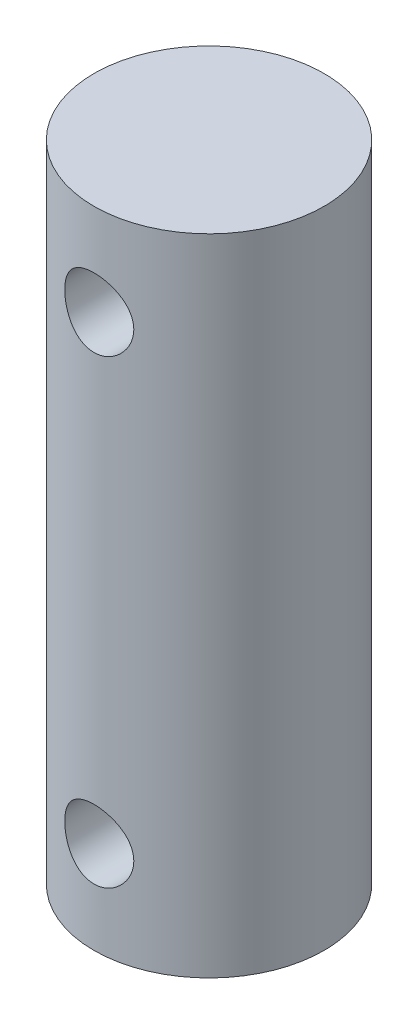
SolidWorks part; units mm, degrees
ref_plane "Front Plane" through (0, 0, 0) normal (0, 0, 1) x (1, 0, 0)
ref_plane "Top Plane" through (0, 0, 0) normal (0, 1, 0) x (1, 0, 0)
ref_plane "Right Plane" through (0, 0, 0) normal (1, 0, 0) x (0, 0, -1)
sketch "Sketch1" plane through (0, 0, 0) normal (0, 1, 0) x (1, 0, 0)
  circle A0 centre (0, 0) radius 4.9995
  dimension "D1" = 9.999
extrude "Boss-Extrude1" add sketch "Sketch1" along normal blind 28
sketch "Sketch2" plane through (0, 0, 0) normal (0, 0, 1) x (1, 0, 0)
  circle A0 centre (0, 4) radius 1.5
  circle A1 centre (0, 24) radius 1.5
extrude "Cut-Extrude1" cut sketch "Sketch2" against normal through all both and the other way through all
